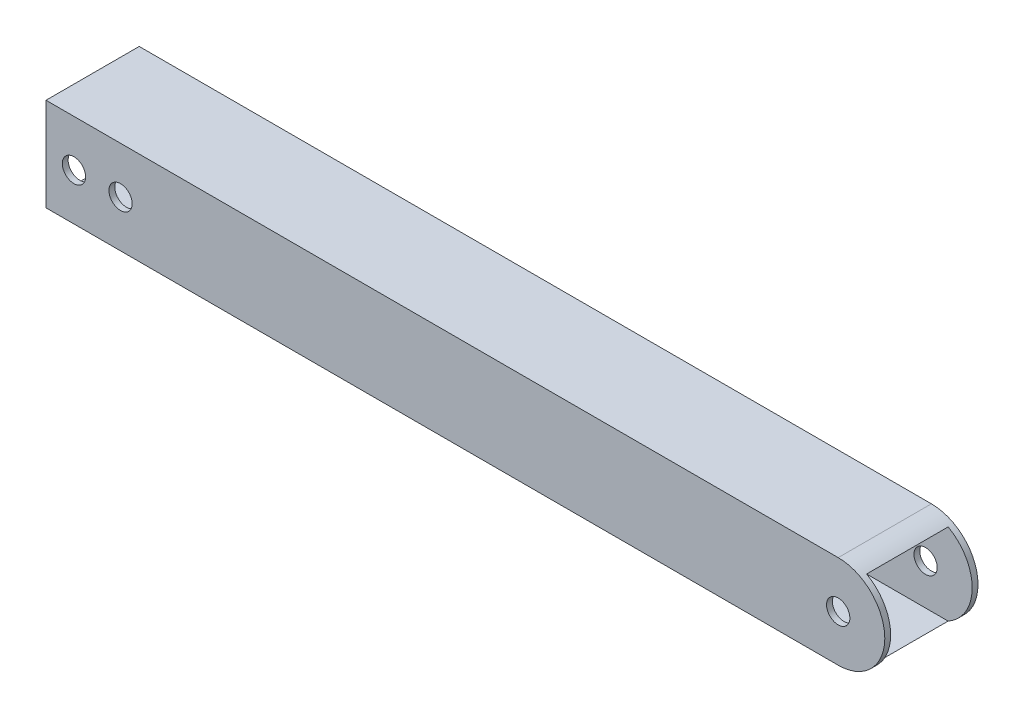
SolidWorks part; units mm, degrees
ref_plane "Front Plane" through (0, 0, 0) normal (0, 0, 1) x (1, 0, 0)
ref_plane "Top Plane" through (0, 0, 0) normal (0, 1, 0) x (1, 0, 0)
ref_plane "Right Plane" through (0, 0, 0) normal (1, 0, 0) x (0, 0, -1)
sketch "Sketch1" plane through (0, 0, 0) normal (1, 0, 0) x (0, 0, -1)
  line L0 (-11.1125, 11.1125) -> (11.1125, 11.1125)
  line L1 (-12.7, 12.7) -> (12.7, 12.7)
  line L2 (-12.7, 12.7) -> (-12.7, -12.7)
  line L3 (-12.7, -12.7) -> (12.7, -12.7)
  line L4 (12.7, 12.7) -> (12.7, -12.7)
  line L5 (-12.7, 12.7) -> (12.7, -12.7) construction
  line L6 (-12.7, -12.7) -> (12.7, 12.7) construction
  line L7 (11.1125, 11.1125) -> (11.1125, -11.1125)
  line L8 (-11.1125, -11.1125) -> (11.1125, -11.1125)
  line L9 (-11.1125, 11.1125) -> (-11.1125, -11.1125)
  point P0 (0, 0)
  dimension "D1" = 25.4
  dimension "D2" = 25.4
  dimension "D3" = 1.5875
extrude "Boss-Extrude1" add sketch "Sketch1" along normal blind 228.6
sketch "Sketch2" plane through (0, 0, 12.7) normal (0, 0, 1) x (1, 0, 0)
  line L0 (228.6, 12.7) -> (0, 12.7) construction
  line L1 (228.6, 12.7) -> (228.6, -12.7) construction
  line L2 (228.6, -12.7) -> (0, -12.7) construction
  circle A0 centre (215.9, 0) radius 3.175
  circle A1 centre (7.62, 0) radius 3.175
  circle A2 centre (20.32, 0) radius 3.175
  dimension "D1" = 6.35
  dimension "D4" = 6.35
  dimension "D5" = 6.35
  dimension "D2" = 12.7
  dimension "D3" = 12.7
  dimension "D6" = 7.62
  dimension "D7" = 12.7
  dimension "D8" = 12.7
  dimension "D9" = 12.7
extrude "Cut-Extrude1" cut sketch "Sketch2" against normal through all
sketch "Sketch3" plane through (0, 0, 12.7) normal (0, 0, 1) x (1, 0, 0)
  line L0 (228.6, 12.7) -> (228.6, -12.7) construction
  line L1 (228.6, 12.7) -> (215.9, 12.7) construction
  line L2 (228.6, 12.7) -> (0, 12.7) construction
  line L3 (215.9, 12.7) -> (215.9, -12.7) construction
  line L4 (228.6, -12.7) -> (0, -12.7) construction
  line L5 (215.9, 12.7) -> (228.6, 12.7)
  line L6 (228.6, 12.7) -> (228.6, -12.7)
  line L7 (228.6, -12.7) -> (215.9, -12.7)
  arc A4 (215.9, 12.7) -> (215.9, -12.7) centre (215.9, 0) cw
  point P5 (228.6, -12.7)
  line M7 (0, -12.7) -> (228.6, -12.7)
  line M8 (228.6, -12.7) -> (228.6, 12.7)
  line M9 (228.6, 12.7) -> (0, 12.7)
  dimension "0.5" = 12.7
extrude "Cut-Extrude2" cut sketch "Sketch3" against normal through all contours A4 L6 M9 | A4 M8 M7
